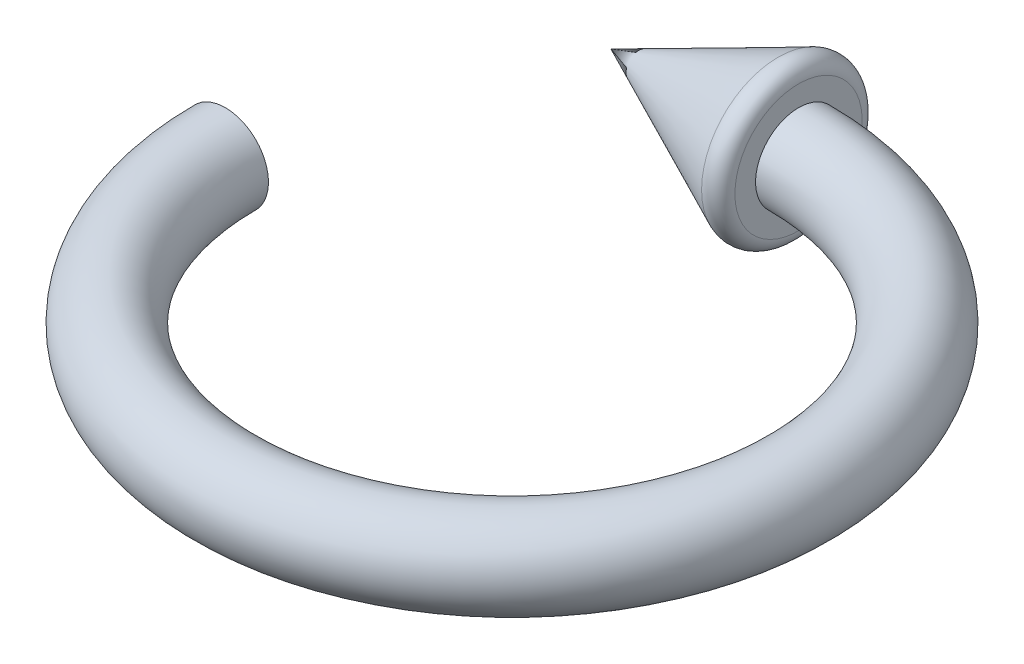
SolidWorks part; units mm, degrees
ref_plane "Front Plane" through (0, 0, 0) normal (0, 0, 1) x (1, 0, 0)
ref_plane "Top Plane" through (0, 0, 0) normal (0, 1, 0) x (1, 0, 0)
ref_plane "Right Plane" through (0, 0, 0) normal (1, 0, 0) x (0, 0, -1)
sketch "Sketch1" plane through (0, 0, 0) normal (0, 1, 0) x (1, 0, 0)
  arc A0 (-200, 0) -> (0, 200) centre (0, 0) ccw
  dimension "D1" = 200
sketch "Sketch2" plane through (0, 0, 0) normal (0, 0, 1) x (1, 0, 0)
  line L0 (200, 0) -> (-200, 0) construction
  circle A0 centre (-200, 0) radius 30
  dimension "D1" = 60
sweep "Sweep1" add profiles "Sketch2" path "Sketch1"
sketch "Sketch3" plane through (0, 0, 0) normal (0, 1, 0) x (1, 0, 0)
  line L0 (0, 200) -> (0, 140)
  line L1 (0, 230) -> (0, 170) construction
  line L2 (0, 140) -> (-130.9694, 200)
  line L3 (-130.9694, 200) -> (0, 200)
  line L4 (0, 200) -> (-0.9998, 200.9531)
  dimension "D1" = 60
  dimension "D2" = 130.9694
revolve "Revolve2" add sketch "Sketch3" angle 360 about L3
fillet "Fillet1" radius 10 1 edges at (0, 0, -140)
